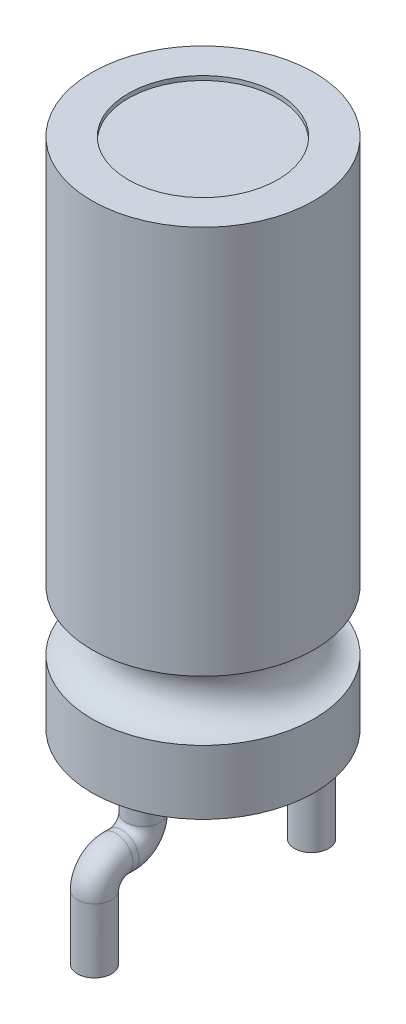
SolidWorks part; units mm, degrees
ref_plane "Face" through (0, 0, 0) normal (0, 0, 1) x (1, 0, 0)
ref_plane "Dessus" through (0, 0, 0) normal (0, 1, 0) x (1, 0, 0)
ref_plane "Droite" through (0, 0, 0) normal (1, 0, 0) x (0, 0, -1)
sketch "Esquisse1" plane through (0, 0, 0) normal (0, 0, 1) x (1, 0, 0)
  line L0 (0, 48.4017) -> (0, -33.7592) construction
  line L1 (0, 39.5164) -> (2.6, 39.5164)
  line L2 (2.6, 39.5164) -> (2.6, 30.4164)
  line L3 (2.6, 29.0164) -> (2.6, 27.5164)
  line L4 (2.6, 27.5164) -> (0, 27.5164)
  line L5 (0, 27.5164) -> (0, 39.5164)
  line L6 (9.8114, 29.7164) -> (-7.1309, 29.7164) construction
  line L7 (2.6, 25.0819) -> (2.6, 32.6721) construction
  line L8 (5.1241, 27.5164) -> (-5.6865, 27.5164) construction
  line L9 (5.1241, 29.0164) -> (-3.1767, 29.0164) construction
  arc A0 (2.6, 30.4164) -> (2.6, 29.0164) centre (2.6, 29.7164) ccw
  dimension "D4" = 0.7
  dimension "D1" = 12
  dimension "D2" = 2.6
  dimension "D3" = 1.5
revolve "Révolution1" add sketch "Esquisse1" angle 360 about L0
sketch "Esquisse2" plane through (0, 39.5164, 0) normal (0, 1, 0) x (-1, 0, 0)
  circle A0 centre (0, 0) radius 1.75
  dimension "D1" = 3.5
extrude "Enlèv. mat.-Extru.1" cut sketch "Esquisse2" against normal blind 0.1
sketch "Esquisse3" plane through (0, 27.5164, 0) normal (0, -1, 0) x (1, 0, 0)
  line L0 (4.0351, 0) -> (-4.283, 0) construction
  line L1 (0, 6.7464) -> (0, -6.9013) construction
  circle A0 centre (0, 1.4) radius 0.4
  dimension "D1" = 0.8
sketch "Esquisse4" plane through (0, 0, 0) normal (1, 0, 0) x (0, 0, -1)
  line L0 (-1.4, 24.8484) -> (-1.4, 29.3314) construction
  line L1 (-5.5325, 26.0164) -> (6.9013, 26.0164) construction
  line L2 (-2.54, 26.4376) -> (-2.54, 18.8472) construction
  line L3 (-8.7913, 27.5164) -> (10.5025, 27.5164) construction
  line L4 (0, 26.7733) -> (0, 22.2147) construction
  line L5 (-6.5666, 24.0164) -> (9.3213, 24.0164) construction
  line L6 (-1.4, 27.5164) -> (-1.4, 26.5164)
  line L7 (-1.9, 26.0164) -> (-2.04, 26.0164)
  line L8 (-2.54, 25.5164) -> (-2.54, 24.0164)
  arc A0 (-1.4, 26.5164) -> (-1.9, 26.0164) centre (-1.9, 26.5164) cw
  arc A1 (-2.04, 26.0164) -> (-2.54, 25.5164) centre (-2.04, 25.5164) ccw
  dimension "D4" = 0.5
  dimension "D1" = 1.5
  dimension "D2" = 2.54
  dimension "D3" = 2
sweep "Balayage2" add profiles "Esquisse3" path "Esquisse4"
sketch "Esquisse6" plane through (0, 27.5164, 0) normal (0, -1, 0) x (1, 0, 0)
  line L0 (-3.2602, 0) -> (3.5913, 0) construction
  line L1 (0, -3.1685) -> (0, 0.6531) construction
  line L2 (-2.9426, -1.4) -> (3.3345, -1.4) construction
  circle A0 centre (0, -1.4) radius 0.4
  dimension "D1" = 1.4
sketch "Esquisse7" plane through (0, 0, 0) normal (1, 0, 0) x (0, 0, -1)
  line L0 (1.4, 28.1391) -> (1.4, 25.342) construction
  line L1 (0.6547, 26.0164) -> (4.064, 26.0164) construction
  line L2 (2.54, 26.6508) -> (2.54, 23.231) construction
  line L3 (-0.918, 24.0164) -> (4.8028, 24.0164) construction
  line L4 (0, 28.1391) -> (0, 23.3049) construction
  line L5 (2.7763, 27.5164) -> (-4.5278, 27.5164) construction
  line L6 (1.4, 27.5164) -> (1.4, 26.5164)
  line L7 (1.9, 26.0164) -> (2.04, 26.0164)
  line L8 (2.54, 25.5164) -> (2.54, 24.0164)
  arc A0 (1.4, 26.5164) -> (1.9, 26.0164) centre (1.9, 26.5164) ccw
  arc A1 (2.04, 26.0164) -> (2.54, 25.5164) centre (2.04, 25.5164) cw
  dimension "D4" = 0.5
  dimension "D1" = 1.5
  dimension "D2" = 2.54
  dimension "D3" = 2
sweep "Balayage3" add profiles "Esquisse6" path "Esquisse7"
